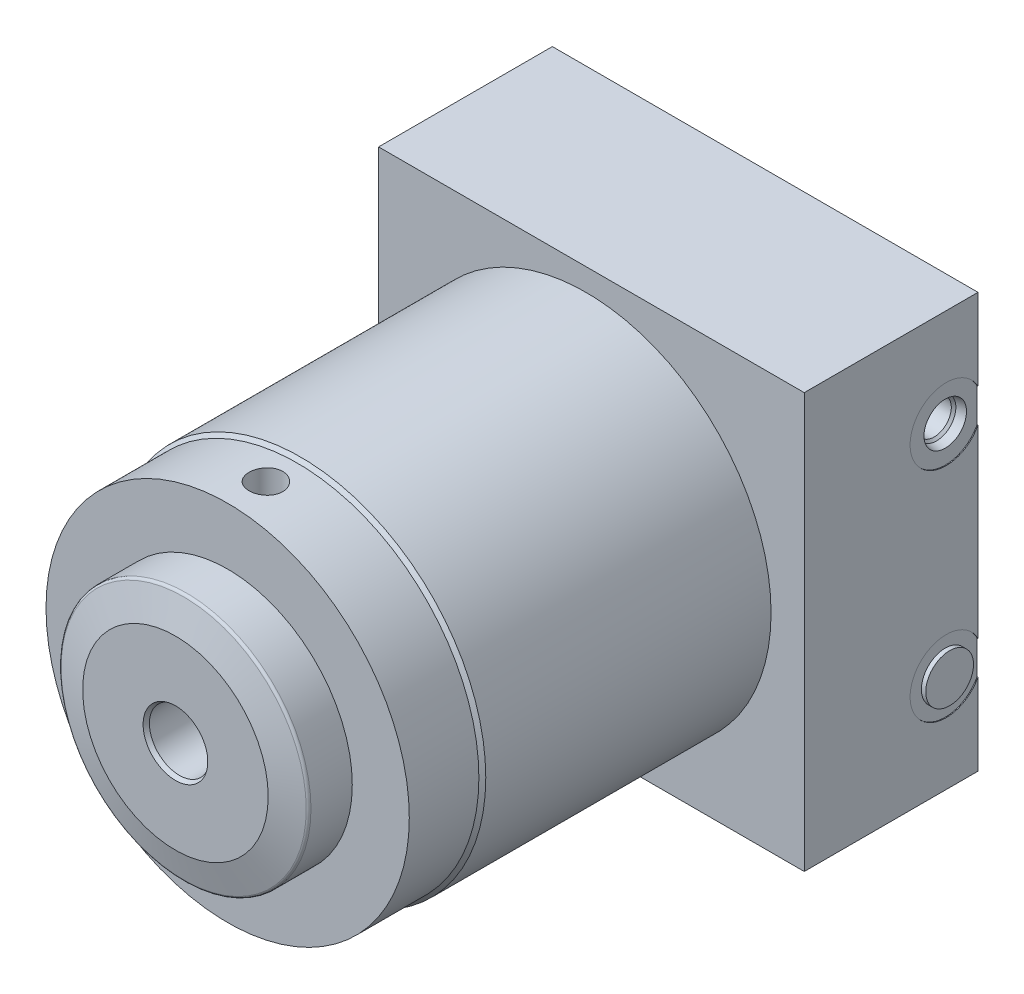
SolidWorks part; units mm, degrees
material "Alloy Steel"
ref_plane "Front Plane" through (0, 0, 0) normal (0, 0, 1) x (1, 0, 0)
ref_plane "Top Plane" through (0, 0, 0) normal (0, 1, 0) x (1, 0, 0)
ref_plane "Right Plane" through (0, 0, 0) normal (1, 0, 0) x (0, 0, -1)
ref_plane "Plane1" through (0, 0, 0) normal (0, 0, 1) x (1, 0, 0)
sketch "Sketch1" plane through (0, 0, 0) normal (0, 0, 1) x (1, 0, 0)
  circle A0 centre (0, 0) radius 53.848
  dimension "D1" = 107.696
extrude "Extrude1" add sketch "Sketch1" along normal blind 127.7874
ref_plane "Plane2" through (0, 0, 0) normal (1, 0, 0) x (0, 0, 1)
ref_plane "Plane12" through (0, 0, 0) normal (1, 0, 0) x (0, 0, -1)
sketch "Sketch10" plane through (0, 0, 0) normal (1, 0, 0) x (0, 0, -1)
  line L0 (-127.7874, 52.8447) -> (-107.5436, 52.8447)
  line L1 (-107.5436, 52.8447) -> (-106.5403, 53.848)
  line L2 (-106.5403, 53.848) -> (-127.7874, 53.848)
  line L3 (-127.7874, 53.848) -> (-127.7874, 52.8447)
  line L4 (-160.0822, 0) -> (-81.6616, 0) construction
  line L5 (-127.7874, 53.848) -> (-127.7874, -53.848) construction
  dimension "D1" = 105.6894
  dimension "D2" = 20.2438
  dimension "D3" = 45
revolve "Cut-Revolve1" cut sketch "Sketch10" angle 360 about L4
ref_plane "Plane15" through (0, 0, 0) normal (1, 0, 0) x (0, 0, -1)
sketch "Sketch13" plane through (0, 0, 0) normal (1, 0, 0) x (0, 0, -1)
  line L0 (-127.7874, 0) -> (-142.9766, 0)
  line L1 (-142.9766, 0) -> (-142.9766, 36.2585)
  line L2 (-142.9766, 36.2585) -> (-127.7874, 36.2585)
  line L3 (-127.7874, 36.2585) -> (-127.7874, 0)
  line L4 (-113.599, 0) -> (-63.8453, 0) construction
  line L5 (-127.7874, 52.8447) -> (-127.7874, -52.8447) construction
  dimension "D1" = 15.1892
  dimension "D2" = 72.517
revolve "Revolve1" add sketch "Sketch13" angle 360 about L4
ref_plane "Plane16" through (-6.9342, 0, 112.8014) normal (0, 1, 0) x (-1, 0, 0)
sketch "S2D0011" plane through (-6.9342, 0, 112.8014) normal (0, 1, 0) x (-1, 0, 0)
  line L0 (1.8034, 30.1752) -> (1.8034, 12.1412)
  line L1 (1.8034, 12.1412) -> (-6.9342, 12.1412)
  line L2 (1.8034, 30.1752) -> (-6.9342, 30.1752)
  line L3 (-6.9342, 30.1752) -> (-6.9342, 12.1412)
  line L4 (-6.9342, -6.2611) -> (-6.9342, 0.8001) construction
  line L5 (-60.7822, -6.2611) -> (46.9138, -6.2611) construction
  line L6 (29.3243, 30.1752) -> (-43.1927, 30.1752) construction
  dimension "D1" = 17.4752
  dimension "D2" = 18.034
revolve "Cut-Revolve4" cut sketch "S2D0011" angle 360 about L4
ref_plane "Plane17" through (0, 0, 0) normal (1, 0, 0) x (0, 0, -1)
sketch "Sketch15" plane through (0, 0, 0) normal (1, 0, 0) x (0, 0, -1)
  line L0 (-142.9766, 26.9875) -> (-140.5852, 35.6617)
  line L1 (-112.9602, 0) -> (-109.4676, 0) construction
  line L2 (-142.9766, 36.2585) -> (-142.9766, 26.9875)
  line L3 (-139.8016, 36.2585) -> (-142.9766, 36.2585)
  arc A0 (-139.8016, 36.2585) -> (-140.5852, 35.6617) centre (-139.8016, 35.4457) ccw
  dimension "D2" = 0.8128
  dimension "D1" = 3.175
  dimension "D3" = 53.975
revolve "Cut-Revolve5" cut sketch "Sketch15" angle 360 about L1
ref_plane "Plane18" through (0, 0, 0) normal (0, 1, 0) x (-1, 0, 0)
sketch "Sketch16" plane through (0, 0, 0) normal (0, 1, 0) x (-1, 0, 0)
  line L0 (-63.5, -27.0002) -> (60.325, -27.0002)
  line L1 (60.325, -27.0002) -> (60.325, 23.5458)
  line L2 (60.325, 23.5458) -> (-63.5, 23.5458)
  line L3 (-63.5, 23.5458) -> (-63.5, -27.0002)
  line L4 (-53.848, 0) -> (53.848, 0) construction
  dimension "D1" = 27.0002
  dimension "D2" = 50.546
  dimension "D3" = 123.825
  dimension "D4" = 60.325
extrude "Extrude2" add sketch "Sketch16" along normal mid plane 120.65
sketch "Sketch17" plane through (63.5, 0, 0) normal (1, 0, 0) x (0, 0, -1)
  line L0 (27.0002, -60.325) -> (27.0002, 60.325) construction
  circle A0 centre (17.7292, -31.75) radius 10.4775
  dimension "D2" = 20.955
  dimension "D3" = 9.271
  dimension "D1" = 31.75
extrude "Cut-Extrude9" cut sketch "Sketch17" against normal blind 0.254
sketch "Sketch18" plane through (63.5, 0, 0) normal (1, 0, 0) x (0, 0, -1)
  line L0 (27.0002, -26.8688) -> (27.0002, 60.325) construction
  circle A0 centre (17.7292, 31.75) radius 10.4775
  dimension "D1" = 20.955
  dimension "D3" = 31.75
  dimension "D2" = 9.271
extrude "Cut-Extrude10" cut sketch "Sketch18" against normal blind 0.254
ref_plane "Plane21" through (0, 0, -17.7292) normal (0, 0, -1) x (-1, 0, 0)
sketch "S2D0001" plane through (52.1462, 23.8125, -17.7292) normal (0, 0, 1) x (0, -1, 0)
  line L0 (-7.9375, 11.0998) -> (-1.7526, 11.0998)
  line L1 (-1.7526, 11.0998) -> (-2.2952, 8.5471)
  line L2 (-2.2952, 8.5471) -> (-2.9591, 7.8832)
  line L3 (-2.9591, 7.8832) -> (-2.9591, -6.1722)
  line L4 (-2.9591, -6.1722) -> (-7.9375, -6.1722)
  line L5 (-7.9375, -6.1722) -> (-7.9375, 11.0998)
  line L6 (-7.9375, -18.1356) -> (-7.9375, 0.8636) construction
  line L8 (-12.8187, 11.0998) -> (-3.0563, 11.0998) construction
  dimension "D1" = 17.272
  dimension "D2" = 4.9784
  dimension "D3" = 135
  dimension "D4" = 12
  dimension "D5" = 12.3698
  dimension "D6" = 3.2166
  dimension "D7" = 31.75
revolve "Cut-Revolve7" cut sketch "S2D0001" angle 360 about L6
sketch "Sketch21" plane through (63.246, 0, 0) normal (1, 0, 0) x (0, 0, -1)
  circle A0 centre (17.7292, -31.75) radius 6.9469
  arc A1 (27.0002, -26.8688) -> (27.0002, -36.6312) centre (17.7292, -31.75) ccw construction
  dimension "D1" = 13.8938
extrude "Extrude3" add sketch "Sketch21" along normal blind 1.27
chamfer "Chamfer1" distance 1.1684 angle 30 1 edges at (-8.7376, 0, 142.9766)
sketch "Sketch23" plane through (0, 0, 0) normal (1, 0, 0) x (0, 0, -1)
  line L0 (-116.6622, 62.1638) -> (-116.6622, -63.3497) construction
  line L1 (-121.5517, 52.8447) -> (-121.5517, 44.9707)
  line L2 (-107.5436, 52.8447) -> (-127.7874, 52.8447) construction
  line L3 (-121.5517, 44.9707) -> (-116.6622, 42.0328)
  line L4 (-116.6622, 42.0328) -> (-116.6622, 52.8447)
  line L5 (-116.6622, 52.8447) -> (-121.5517, 52.8447)
  line L6 (-127.7874, 52.8447) -> (-127.7874, -52.8447) construction
  dimension "D1" = 11.1252
  dimension "D2" = 9.779
  dimension "D3" = 7.874
  dimension "D4" = 59
revolve "Cut-Revolve8" cut sketch "Sketch23" angle 360 about L0
mirror "Mirror1" about plane through (0, 0, 0) normal (0, 1, 0) of "Cut-Revolve8"
